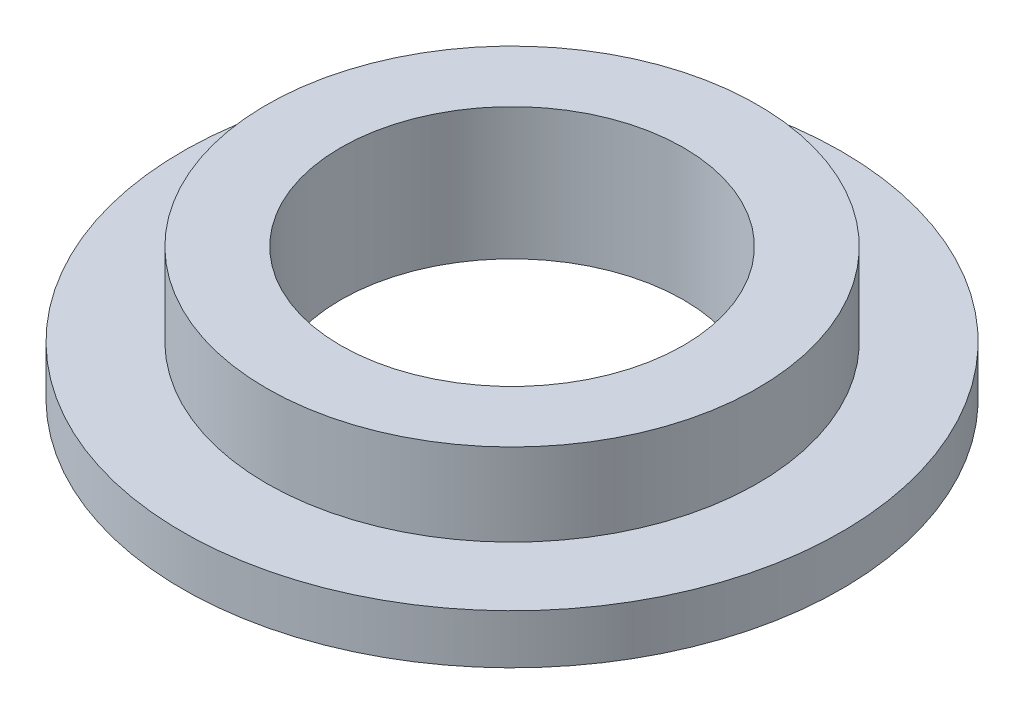
SolidWorks part; units mm, degrees
ref_plane "前视基准面" through (0, 0, 0) normal (0, 0, 1) x (1, 0, 0)
ref_plane "上视基准面" through (0, 0, 0) normal (0, 1, 0) x (1, 0, 0)
ref_plane "右视基准面" through (0, 0, 0) normal (1, 0, 0) x (0, 0, -1)
other "Configuration Table"
sketch "草图1" plane through (0, 0, 0) normal (0, 1, 0) x (1, 0, 0)
  circle A0 centre (0, 0) radius 10.4
  circle A1 centre (0, 0) radius 14.9
  dimension "D1" = 20.8
  dimension "D2" = 29.8
extrude "凸台-拉伸1" add sketch "草图1" along normal blind 5
sketch "草图2" plane through (0, 0, 0) normal (0, -1, 0) x (1, 0, 0)
  circle A0 centre (0, 0) radius 20
  circle A1 centre (0, 0) radius 10.4 construction
  circle A2 centre (0, 0) radius 10.4
  dimension "D1" = 40
extrude "凸台-拉伸2" add sketch "草图2" along normal blind 3
